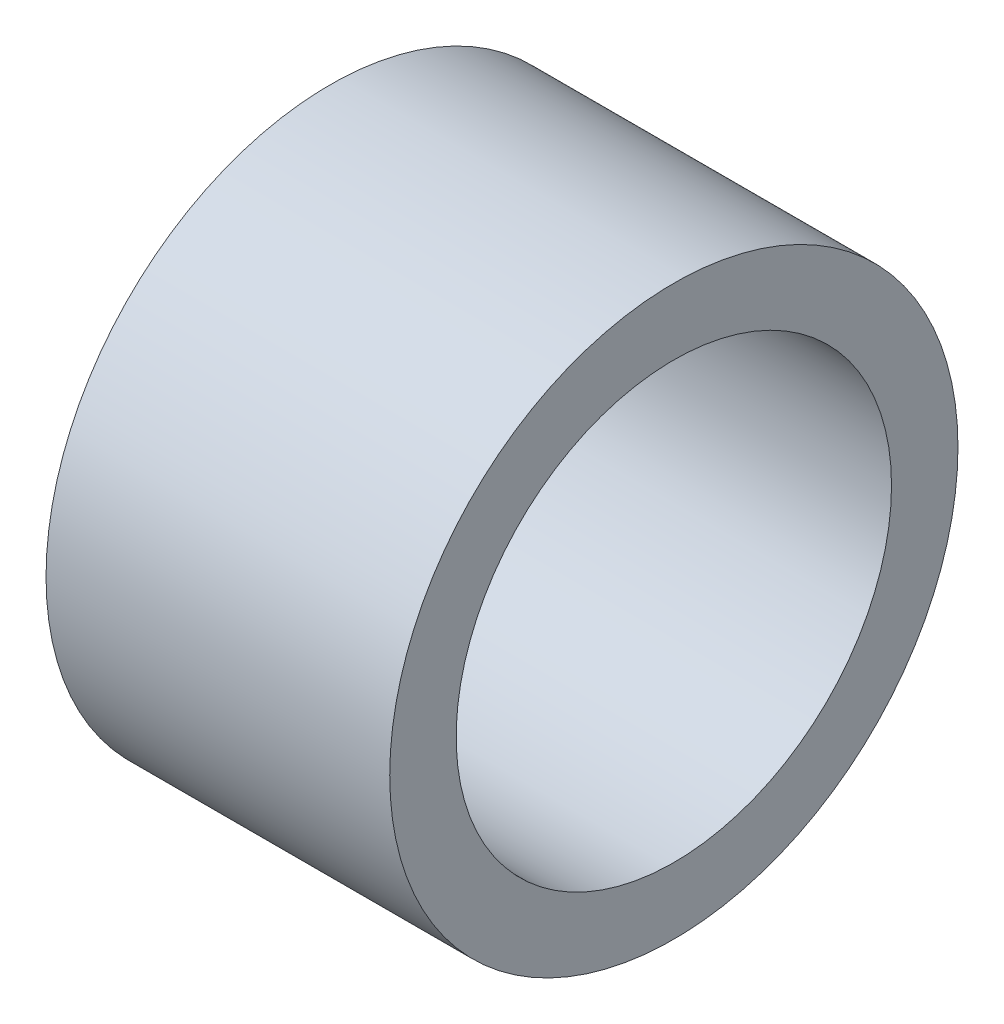
SolidWorks part; units mm, degrees
ref_plane "Front" through (0, 0, 0) normal (0, 0, 1) x (1, 0, 0)
ref_plane "Top" through (0, 0, 0) normal (0, 1, 0) x (1, 0, 0)
ref_plane "Right" through (0, 0, 0) normal (1, 0, 0) x (0, 0, -1)
sketch "Sketch1" plane through (0, 0, 0) normal (0, 0, 1) x (1, 0, 0)
  line L0 (0, 4.75) -> (0, 6.2)
  line L1 (0, 6.2) -> (-4, 6.2)
  line L6 (-7.5, 6.2) -> (-7.5, 4.75)
  line L7 (-7.5, 4.75) -> (0, 4.75)
  line L8 (0, 0) -> (-8.0706, 0) construction
  line L9 (-4, 6.2) -> (-7.5, 6.2)
  dimension "D1" = 4.75
  dimension "D2" = 6.2
  dimension "D7" = 7.5
revolve "Base-Revolve" add sketch "Sketch1" angle 360 about L8
